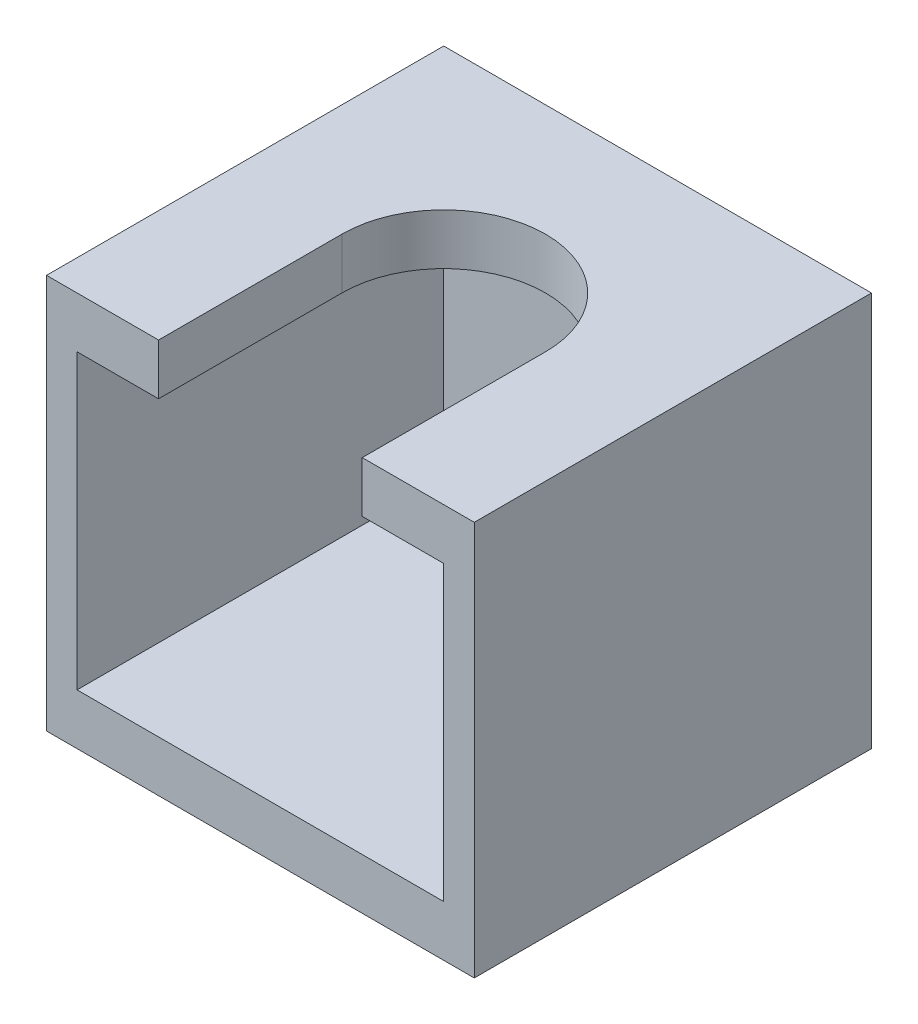
SolidWorks part; units mm, degrees
ref_plane "Front Plane" through (0, 0, 0) normal (0, 0, 1) x (1, 0, 0)
ref_plane "Top Plane" through (0, 0, 0) normal (0, 1, 0) x (1, 0, 0)
ref_plane "Right Plane" through (0, 0, 0) normal (1, 0, 0) x (0, 0, -1)
sketch "Sketch1" plane through (0, 0, 0) normal (0, 1, 0) x (1, 0, 0)
  line L0 (-8.4, 8.4) -> (-8.4, -7.2)
  line L1 (-7.2, 7.2) -> (7.2, 7.2)
  line L2 (-7.2, 7.2) -> (-7.2, -7.2)
  line L3 (-7.2, -7.2) -> (7.2, -7.2) construction
  line L4 (7.2, 7.2) -> (7.2, -7.2)
  line L5 (-7.2, 7.2) -> (7.2, -7.2) construction
  line L6 (-7.2, -7.2) -> (7.2, 7.2) construction
  line L8 (8.4, 8.4) -> (8.4, -7.2)
  line L9 (-8.4, 8.4) -> (8.4, 8.4)
  line L10 (-8.4, -8.4) -> (8.4, -8.4) construction
  line L11 (-7.2, -7.2) -> (-8.4, -7.2)
  line L12 (7.2, -7.2) -> (8.4, -7.2)
  line L13 (-8.4, 8.4) -> (-8.4, -8.4) construction
  line L14 (8.4, 8.4) -> (8.4, -8.4) construction
  point P0 (0, 0)
  dimension "D1" = 14.4
  dimension "D2" = 1.2
extrude "Boss-Extrude1" add sketch "Sketch1" along normal blind 11.5
sketch "Sketch2" plane through (0, 0, 0) normal (0, -1, 0) x (1, 0, 0)
  line L1 (-8.4, 7.2) -> (8.4, 7.2)
  line L2 (-8.4, 7.2) -> (-8.4, -8.4)
  line L3 (-8.4, -8.4) -> (8.4, -8.4)
  line L4 (8.4, 7.2) -> (8.4, -8.4)
extrude "Boss-Extrude2" add sketch "Sketch2" along normal blind 2
sketch "Sketch3" plane through (0, 11.5, 0) normal (0, 1, 0) x (1, 0, 0)
  line L0 (-4, 0) -> (-4, -7.2)
  line L1 (-8.4, 8.4) -> (8.4, 8.4)
  line L2 (-8.4, 8.4) -> (-8.4, -7.2)
  line L3 (-8.4, -7.2) -> (-4, -7.2)
  line L4 (8.4, 8.4) -> (8.4, -7.2)
  line L5 (4, 0) -> (4, -7.2)
  line L6 (7.2, -7.2) -> (-7.2, -7.2) construction
  line L7 (4, -7.2) -> (8.4, -7.2)
  arc A0 (-4, 0) -> (4, 0) centre (0, 0) cw
  dimension "D1" = 4
extrude "Boss-Extrude3" add sketch "Sketch3" along normal blind 2
